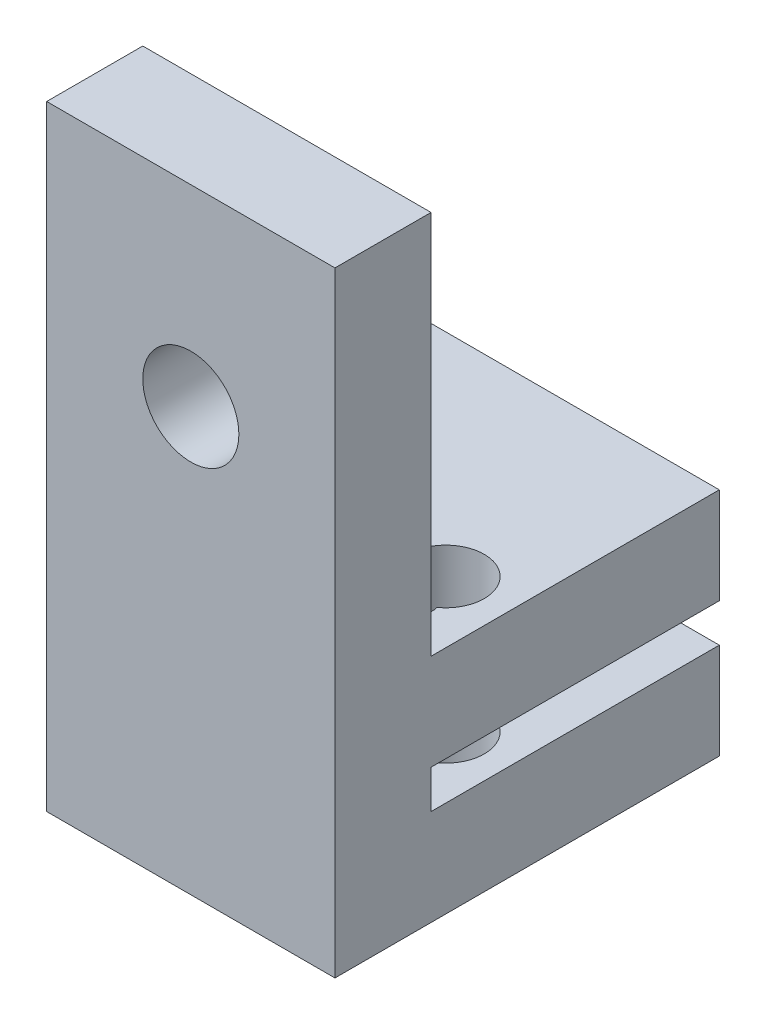
SolidWorks part; units mm, degrees
ref_plane "Piano frontale" through (0, 0, 0) normal (0, 0, 1) x (1, 0, 0)
ref_plane "Piano superiore" through (0, 0, 0) normal (0, 1, 0) x (1, 0, 0)
ref_plane "Piano destro" through (0, 0, 0) normal (1, 0, 0) x (0, 0, -1)
sketch "Schizzo1" plane through (0, 0, 0) normal (1, 0, 0) x (0, 0, -1)
  line L0 (52901.8461, -245.4423) -> (52901.8461, -247.4423) construction
  line L1 (0, 0) -> (-20, 0)
  line L2 (-15, 5) -> (-15, 7)
  line L3 (0, 12) -> (-20, 12)
  line L4 (-20, 0) -> (-20, 12)
  line L6 (0, 0) -> (0, 5)
  line L7 (0, 5) -> (-15, 5)
  line L10 (0, 12) -> (0, 7)
  line L11 (0, 7) -> (-15, 7)
  dimension "D1" = 15
  dimension "D2" = 20
  dimension "D3" = 12
extrude "Estrusione-Estrusione1" add sketch "Schizzo1" along normal blind 15
sketch "Schizzo5" plane through (0, 0, 20) normal (0, 0, 1) x (1, 0, 0)
  line L0 (0, 12) -> (0, 0) construction
  line L1 (15, 32) -> (0, 32)
  line L2 (15, 32) -> (15, 12)
  line L3 (15, 12) -> (0, 12)
  line L4 (0, 32) -> (0, 12)
  line L5 (15, 32) -> (0, 12) construction
  line L6 (15, 12) -> (0, 32) construction
  line L7 (15, 12) -> (15, 0) construction
  line L8 (15, 12) -> (0, 12) construction
  circle A0 centre (7.5, 22) radius 2.5
  dimension "D1" = 5
  dimension "D2" = 20
extrude "Estrusione-Estrusione2" add sketch "Schizzo5" against normal up to surface (5 mm away) up to face at (7.5, 6, 15)
sketch "Schizzo6" plane through (0, 0, 0) normal (0, -1, 0) x (1, 0, 0)
  line L0 (7.5, 20) -> (7.5, -4.7288) construction
  line L1 (15, 20) -> (0, 20) construction
  circle A0 centre (3.2115, 11.0216) radius 2
  circle A1 centre (11.7885, 11.0216) radius 2
  dimension "D1" = 4
extrude "Taglio-Estrusione2" cut sketch "Schizzo6" against normal up to surface (12 mm away) up to face at (7.5, 12, 7.5)
sketch "Schizzo4" plane through (0, 0, 0) normal (0, -1, 0) x (1, 0, 0)
  line L0 (7.5, 20) -> (7.5, 0) construction
  line L2 (15, 20) -> (0, 20) construction
  line L3 (15, 0) -> (0, 0) construction
  circle A0 centre (3.5, 13) radius 1.5
  circle A1 centre (11.5, 13) radius 1.5
  dimension "D1" = 3
  dimension "D2" = 8
  dimension "D3" = 7
extrude "Taglio-Estrusione1" cut sketch "Schizzo4" against normal up to surface (12 mm away) up to face at (3.2115, 12, 9.0216)
